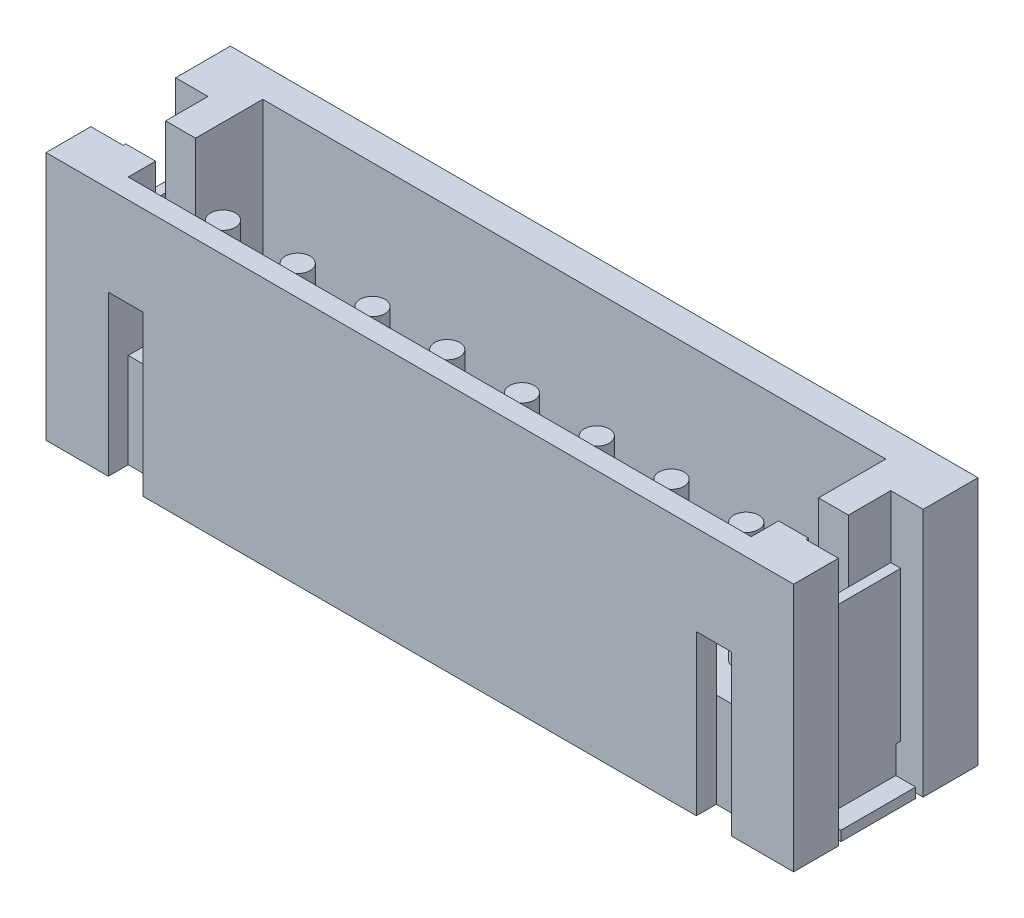
SolidWorks part; units mm, degrees
ref_plane "Front Plane" through (0, 0, 0) normal (0, 0, 1) x (1, 0, 0)
ref_plane "Top Plane" through (0, 0, 0) normal (0, 1, 0) x (1, 0, 0)
ref_plane "Right Plane" through (0, 0, 0) normal (1, 0, 0) x (0, 0, -1)
sketch "Sketch1" plane through (0, 0, 0) normal (0, 0, 1) x (1, 0, 0)
  line L0 (-7.5, 0) -> (-6.25, 0)
  line L1 (-6.25, 0) -> (-6.25, 5)
  line L2 (-6.25, 5) -> (-7.5, 5)
  line L3 (-7.5, 5) -> (-7.5, 0)
extrude "Boss-Extrude1" add sketch "Sketch1" against normal blind 3.1
sketch "Sketch2" plane through (-6.25, 0, 0) normal (1, 0, 0) x (0, 0, -1)
  line L0 (0, 5) -> (0.4, 5)
  line L1 (0.4, 5) -> (0.4, 1.9)
  line L2 (0.4, 1.9) -> (1.75, 1.9)
  line L3 (1.75, 1.9) -> (2.05, 1.6)
  line L4 (2.05, 1.6) -> (3.1, 1.6)
  line L5 (3.1, 0) -> (0, 0)
  line L6 (0, 0) -> (0, 5)
  spline S0 degree 1 poles (3.1, 0) (3.1, 1.6) knots 0 0 0.32 0.32
extrude "Boss-Extrude2" add sketch "Sketch2" along normal blind 12.5
sketch "Sketch3" plane through (6.25, 0, 0) normal (1, 0, 0) x (0, 0, -1)
  line L0 (3.1, 0) -> (0, 0)
  line L1 (0, 0) -> (0, 5)
  line L2 (0, 5) -> (3.1, 5)
  spline S0 degree 1 poles (3.1, 0) (3.1, 5) knots 0 0 1 1
extrude "Boss-Extrude3" add sketch "Sketch3" along normal blind 1.25
ref_plane "Plane1" through (6.25, 0, 0) normal (1, 0, 0) x (0, 0, -1)
sketch "Sketch4" plane through (6.25, 0, 0) normal (1, 0, 0) x (0, 0, -1)
  line L0 (0.4, 1.9) -> (0.4, 3.2)
  line L1 (0.4, 3.2) -> (0, 3.2)
  line L2 (0, 3.2) -> (0, 0)
  line L3 (0, 0) -> (0.4, 0)
  line L4 (0.4, 0) -> (0.4, 1.9)
extrude "Cut-Extrude1" cut sketch "Sketch4" against normal blind 0.7
ref_plane "Plane2" through (-6.25, 0, 0) normal (-1, 0, 0) x (0, -1, 0)
sketch "Sketch5" plane through (-6.25, 0, 0) normal (-1, 0, 0) x (0, -1, 0)
  line L0 (-1.9, -0.4) -> (0, -0.4)
  line L1 (0, -0.4) -> (0, 0)
  line L2 (0, 0) -> (-3.2, 0)
  line L3 (-3.2, 0) -> (-3.2, -0.4)
  line L4 (-3.2, -0.4) -> (-1.9, -0.4)
extrude "Cut-Extrude2" cut sketch "Sketch5" against normal blind 0.7
sketch "Sketch6" plane through (0, 0, -3.1) normal (0, 0, -1) x (-1, 0, 0)
  spline S0 degree 1 poles (7.5, 0) (-7.5, 0) knots 0 0 1 1
  spline S1 degree 1 poles (-7.5, 0) (-7.5, 5) knots 0 0 1 1
  spline S2 degree 1 poles (7.5, 5) (-7.5, 5) knots 0 0 1 1
  spline S3 degree 1 poles (7.5, 0) (7.5, 5) knots 0 0 1 1
extrude "Boss-Extrude4" add sketch "Sketch6" along normal blind 0.6
sketch "Sketch7" plane through (0, 0, 0) normal (0, -1, 0) x (1, 0, 0)
  line L0 (-7.5, -2.6) -> (-7.05, -2.6)
  line L1 (-7.05, -2.6) -> (-7.05, -0.9)
  line L2 (-7.05, -0.9) -> (-7.5, -0.9)
  line L3 (-7.5, -0.9) -> (-7.5, -2.6)
extrude "Cut-Extrude3" cut sketch "Sketch7" against normal through all
sketch "Sketch8" plane through (-7.05, 0, 0) normal (-1, 0, 0) x (0, 0, 1)
  line L0 (-1.75, 5) -> (-1.75, 3.75)
  line L1 (-1.75, 3.75) -> (-0.95, 3.75)
  line L2 (-0.95, 3.75) -> (-0.95, 5)
  line L3 (-0.95, 5) -> (-1.75, 5)
extrude "Cut-Extrude4" cut sketch "Sketch8" against normal up to next
sketch "Sketch9" plane through (-7.05, 0, 0) normal (-1, 0, 0) x (0, 0, 1)
  line L0 (-2.6, 3.75) -> (-1.75, 3.75)
  line L1 (-1.75, 3.75) -> (-1.75, 5)
  line L2 (-1.75, 5) -> (-2.6, 5)
  line L3 (-2.6, 5) -> (-2.6, 3.75)
extrude "Cut-Extrude5" cut sketch "Sketch9" against normal blind 0.2
sketch "Sketch10" plane through (-7.05, 0, 0) normal (-1, 0, 0) x (0, 0, 1)
  line L0 (-0.95, 3.75) -> (-0.9, 3.75)
  line L1 (-0.9, 3.75) -> (-0.9, 5)
  line L2 (-0.9, 5) -> (-0.95, 5)
  line L3 (-0.95, 5) -> (-0.95, 3.75)
extrude "Cut-Extrude6" cut sketch "Sketch10" against normal blind 0.2
ref_plane "Plane3" through (0, 3.75, 0) normal (0, 1, 0) x (1, 0, 0)
ref_plane "Plane4" through (0, 3.2, 0) normal (0, -1, 0) x (1, 0, 0)
sketch "Sketch12" plane through (0, 3.2, 0) normal (0, -1, 0) x (1, 0, 0)
  line L0 (-6.25, -0.95) -> (-6.85, -0.95)
  line L1 (-6.85, -0.95) -> (-6.85, -1.75)
  line L2 (-6.85, -1.75) -> (-6.25, -1.75)
  line L3 (-6.25, -1.75) -> (-6.25, -0.95)
extrude "Cut-Extrude7" cut sketch "Sketch12" against normal up to surface up to plane "Plane3"
sketch "Sketch13" plane through (0, 0, 0) normal (0, -1, 0) x (1, 0, 0)
  line L0 (7.5, -0.9) -> (7.05, -0.9)
  line L1 (7.05, -0.9) -> (7.05, -2.6)
  line L2 (7.05, -2.6) -> (7.5, -2.6)
  line L3 (7.5, -2.6) -> (7.5, -0.9)
extrude "Cut-Extrude8" cut sketch "Sketch13" against normal through all
sketch "Sketch14" plane through (7.05, 0, 0) normal (1, 0, 0) x (0, 0, -1)
  line L0 (0.95, 5) -> (0.95, 3.75)
  line L1 (0.95, 3.75) -> (1.75, 3.75)
  line L2 (1.75, 3.75) -> (1.75, 5)
  line L3 (1.75, 5) -> (0.95, 5)
extrude "Cut-Extrude9" cut sketch "Sketch14" against normal through all
sketch "Sketch15" plane through (7.05, 0, 0) normal (1, 0, 0) x (0, 0, -1)
  line L0 (2.6, 3.75) -> (2.6, 5)
  line L1 (2.6, 5) -> (1.75, 5)
  line L2 (1.75, 5) -> (1.75, 3.75)
  line L3 (1.75, 3.75) -> (2.6, 3.75)
extrude "Cut-Extrude10" cut sketch "Sketch15" against normal blind 0.2
ref_plane "Plane5" through (-7.05, 0, 0) normal (-1, 0, 0) x (0, -1, 0)
ref_plane "Plane6" through (-6.85, 0, 0) normal (1, 0, 0) x (0, 0, -1)
sketch "Sketch17" plane through (-6.85, 0, 0) normal (1, 0, 0) x (0, 0, -1)
  line L0 (1, 0) -> (1, 0.75)
  line L1 (1, 0.75) -> (0.9, 0.75)
  line L2 (0.9, 0.75) -> (0.9, 0)
  line L3 (0.9, 0) -> (1, 0)
extrude "Cut-Extrude11" cut sketch "Sketch17" against normal up to surface up to plane "Plane5"
sketch "Sketch18" plane through (-7.05, 0, 0) normal (-1, 0, 0) x (0, 0, 1)
  line L0 (-1, 0.2) -> (-1, 0)
  line L1 (-1, 0) -> (-2.5, 0)
  line L2 (-2.5, 0) -> (-2.5, 0.2)
  line L3 (-2.5, 0.2) -> (-1, 0.2)
extrude "Boss-Extrude5" add sketch "Sketch18" along normal blind 0.4
sketch "Sketch20" plane through (-6.85, 0, 0) normal (1, 0, 0) x (0, 0, -1)
  line L0 (2.6, 0.75) -> (2.5, 0.75)
  line L1 (2.5, 0.75) -> (2.5, 0)
  line L2 (2.5, 0) -> (2.6, 0)
  line L3 (2.6, 0) -> (2.6, 0.75)
extrude "Cut-Extrude12" cut sketch "Sketch20" against normal up to surface up to plane "Plane5"
ref_plane "Plane7" through (7.05, 0, 0) normal (1, 0, 0) x (0, 0, -1)
ref_plane "Plane8" through (6.85, 0, 0) normal (-1, 0, 0) x (0, -1, 0)
sketch "Sketch22" plane through (6.85, 0, 0) normal (-1, 0, 0) x (0, -1, 0)
  line L0 (0, -2.6) -> (0, -2.5)
  line L1 (0, -2.5) -> (-0.75, -2.5)
  line L2 (-0.75, -2.5) -> (-0.75, -2.6)
  line L3 (-0.75, -2.6) -> (0, -2.6)
extrude "Cut-Extrude13" cut sketch "Sketch22" against normal up to surface up to plane "Plane7"
sketch "Sketch23" plane through (7.05, 0, 0) normal (1, 0, 0) x (0, 0, -1)
  line L0 (1, 0) -> (1, 0.2)
  line L1 (1, 0.2) -> (2.5, 0.2)
  line L2 (2.5, 0.2) -> (2.5, 0)
  line L3 (2.5, 0) -> (1, 0)
extrude "Boss-Extrude6" add sketch "Sketch23" along normal blind 0.4
sketch "Sketch25" plane through (6.85, 0, 0) normal (-1, 0, 0) x (0, -1, 0)
  line L0 (0, -0.9) -> (-0.75, -0.9)
  line L1 (-0.75, -0.9) -> (-0.75, -1)
  line L2 (-0.75, -1) -> (0, -1)
  line L3 (0, -1) -> (0, -0.9)
extrude "Cut-Extrude14" cut sketch "Sketch25" against normal up to surface up to plane "Plane7"
sketch "Sketch26" plane through (7.05, 0, 0) normal (1, 0, 0) x (0, 0, -1)
  line L0 (0.95, 3.75) -> (0.95, 5)
  line L1 (0.95, 5) -> (0.9, 5)
  line L2 (0.9, 5) -> (0.9, 3.75)
  line L3 (0.9, 3.75) -> (0.95, 3.75)
extrude "Cut-Extrude15" cut sketch "Sketch26" against normal blind 0.2
sketch "Sketch28" plane through (0, 3.2, 0) normal (0, -1, 0) x (1, 0, 0)
  line L0 (6.85, -1.75) -> (6.85, -0.95)
  line L1 (6.85, -0.95) -> (6.25, -0.95)
  line L2 (6.25, -0.95) -> (6.25, -1.75)
  line L3 (6.25, -1.75) -> (6.85, -1.75)
extrude "Cut-Extrude16" cut sketch "Sketch28" against normal up to surface up to plane "Plane3"
ref_plane "Plane9" through (0, 0, -1.3) normal (0, 0, -1) x (-1, 0, 0)
sketch "Sketch29" plane through (0, 0, -1.3) normal (0, 0, -1) x (-1, 0, 0)
  line L0 (-5.5, 1.9) -> (-5.25, 1.9)
  line L1 (-5.25, 1.9) -> (-5.25, 4.3)
  line L2 (-5.25, 4.3) -> (-5.5, 4.3)
  line L3 (-5.5, 4.3) -> (-5.5, 1.9)
  line L4 (-5.25, 1.9) -> (-5.25, 4.3) construction
revolve "Revolve1" add sketch "Sketch29" angle 360 about L4
sketch "Sketch30" plane through (0, 0, -1.3) normal (0, 0, -1) x (-1, 0, 0)
  line L0 (-4, 1.9) -> (-3.75, 1.9)
  line L1 (-3.75, 1.9) -> (-3.75, 4.3)
  line L2 (-3.75, 4.3) -> (-4, 4.3)
  line L3 (-4, 4.3) -> (-4, 1.9)
  line L4 (-3.75, 1.9) -> (-3.75, 4.3) construction
revolve "Revolve2" add sketch "Sketch30" angle 360 about L4
sketch "Sketch31" plane through (0, 0, -1.3) normal (0, 0, -1) x (-1, 0, 0)
  line L0 (-2.5, 1.9) -> (-2.25, 1.9)
  line L1 (-2.25, 1.9) -> (-2.25, 4.3)
  line L2 (-2.25, 4.3) -> (-2.5, 4.3)
  line L3 (-2.5, 4.3) -> (-2.5, 1.9)
  line L4 (-2.25, 1.9) -> (-2.25, 4.3) construction
revolve "Revolve3" add sketch "Sketch31" angle 360 about L4
sketch "Sketch32" plane through (0, 0, -1.3) normal (0, 0, -1) x (-1, 0, 0)
  line L0 (-1, 1.9) -> (-0.75, 1.9)
  line L1 (-0.75, 1.9) -> (-0.75, 4.3)
  line L2 (-0.75, 4.3) -> (-1, 4.3)
  line L3 (-1, 4.3) -> (-1, 1.9)
  line L4 (-0.75, 1.9) -> (-0.75, 4.3) construction
revolve "Revolve4" add sketch "Sketch32" angle 360 about L4
sketch "Sketch33" plane through (0, 0, -1.3) normal (0, 0, -1) x (-1, 0, 0)
  line L0 (0.5, 1.9) -> (0.75, 1.9)
  line L1 (0.75, 1.9) -> (0.75, 4.3)
  line L2 (0.75, 4.3) -> (0.5, 4.3)
  line L3 (0.5, 4.3) -> (0.5, 1.9)
  line L4 (0.75, 1.9) -> (0.75, 4.3) construction
revolve "Revolve5" add sketch "Sketch33" angle 360 about L4
sketch "Sketch34" plane through (0, 0, -1.3) normal (0, 0, -1) x (-1, 0, 0)
  line L0 (2, 1.9) -> (2.25, 1.9)
  line L1 (2.25, 1.9) -> (2.25, 4.3)
  line L2 (2.25, 4.3) -> (2, 4.3)
  line L3 (2, 4.3) -> (2, 1.9)
  line L4 (2.25, 1.9) -> (2.25, 4.3) construction
revolve "Revolve6" add sketch "Sketch34" angle 360 about L4
sketch "Sketch35" plane through (0, 0, -1.3) normal (0, 0, -1) x (-1, 0, 0)
  line L0 (3.5, 1.9) -> (3.75, 1.9)
  line L1 (3.75, 1.9) -> (3.75, 4.3)
  line L2 (3.75, 4.3) -> (3.5, 4.3)
  line L3 (3.5, 4.3) -> (3.5, 1.9)
  line L4 (3.75, 1.9) -> (3.75, 4.3) construction
revolve "Revolve7" add sketch "Sketch35" angle 360 about L4
sketch "Sketch36" plane through (0, 0, -1.3) normal (0, 0, -1) x (-1, 0, 0)
  line L0 (5, 1.9) -> (5.25, 1.9)
  line L1 (5.25, 1.9) -> (5.25, 4.3)
  line L2 (5.25, 4.3) -> (5, 4.3)
  line L3 (5, 4.3) -> (5, 1.9)
  line L4 (5.25, 1.9) -> (5.25, 4.3) construction
revolve "Revolve8" add sketch "Sketch36" angle 360 about L4
ref_plane "Plane10" through (0, 0.25, 0) normal (0, -1, 0) x (1, 0, 0)
sketch "Sketch37" plane through (0, 0.25, 0) normal (0, -1, 0) x (1, 0, 0)
  line L0 (5.5, -3.7) -> (5.25, -3.7)
  line L1 (5.25, -3.7) -> (5.25, -5.2)
  line L2 (5.25, -5.2) -> (5.5, -5.2)
  line L3 (5.5, -5.2) -> (5.5, -3.7)
  line L4 (5.25, -3.7) -> (5.25, -5.2) construction
revolve "Revolve9" add sketch "Sketch37" angle 360 about L4
sketch "Sketch38" plane through (0, 0.25, 0) normal (0, -1, 0) x (1, 0, 0)
  line L0 (4, -3.7) -> (3.75, -3.7)
  line L1 (3.75, -3.7) -> (3.75, -5.2)
  line L2 (3.75, -5.2) -> (4, -5.2)
  line L3 (4, -5.2) -> (4, -3.7)
  line L4 (3.75, -3.7) -> (3.75, -5.2) construction
revolve "Revolve10" add sketch "Sketch38" angle 360 about L4
sketch "Sketch39" plane through (0, 0.25, 0) normal (0, -1, 0) x (1, 0, 0)
  line L0 (2.5, -3.7) -> (2.25, -3.7)
  line L1 (2.25, -3.7) -> (2.25, -5.2)
  line L2 (2.25, -5.2) -> (2.5, -5.2)
  line L3 (2.5, -5.2) -> (2.5, -3.7)
  line L4 (2.25, -3.7) -> (2.25, -5.2) construction
revolve "Revolve11" add sketch "Sketch39" angle 360 about L4
sketch "Sketch40" plane through (0, 0.25, 0) normal (0, -1, 0) x (1, 0, 0)
  line L0 (1, -3.7) -> (0.75, -3.7)
  line L1 (0.75, -3.7) -> (0.75, -5.2)
  line L2 (0.75, -5.2) -> (1, -5.2)
  line L3 (1, -5.2) -> (1, -3.7)
  line L4 (0.75, -3.7) -> (0.75, -5.2) construction
revolve "Revolve12" add sketch "Sketch40" angle 360 about L4
sketch "Sketch41" plane through (0, 0.25, 0) normal (0, -1, 0) x (1, 0, 0)
  line L0 (-0.5, -3.7) -> (-0.75, -3.7)
  line L1 (-0.75, -3.7) -> (-0.75, -5.2)
  line L2 (-0.75, -5.2) -> (-0.5, -5.2)
  line L3 (-0.5, -5.2) -> (-0.5, -3.7)
  line L4 (-0.75, -3.7) -> (-0.75, -5.2) construction
revolve "Revolve13" add sketch "Sketch41" angle 360 about L4
sketch "Sketch42" plane through (0, 0.25, 0) normal (0, -1, 0) x (1, 0, 0)
  line L0 (-2, -3.7) -> (-2.25, -3.7)
  line L1 (-2.25, -3.7) -> (-2.25, -5.2)
  line L2 (-2.25, -5.2) -> (-2, -5.2)
  line L3 (-2, -5.2) -> (-2, -3.7)
  line L4 (-2.25, -3.7) -> (-2.25, -5.2) construction
revolve "Revolve14" add sketch "Sketch42" angle 360 about L4
sketch "Sketch43" plane through (0, 0.25, 0) normal (0, -1, 0) x (1, 0, 0)
  line L0 (-3.5, -3.7) -> (-3.75, -3.7)
  line L1 (-3.75, -3.7) -> (-3.75, -5.2)
  line L2 (-3.75, -5.2) -> (-3.5, -5.2)
  line L3 (-3.5, -5.2) -> (-3.5, -3.7)
  line L4 (-3.75, -3.7) -> (-3.75, -5.2) construction
revolve "Revolve15" add sketch "Sketch43" angle 360 about L4
sketch "Sketch44" plane through (0, 0.25, 0) normal (0, -1, 0) x (1, 0, 0)
  line L0 (-5, -3.7) -> (-5.25, -3.7)
  line L1 (-5.25, -3.7) -> (-5.25, -5.2)
  line L2 (-5.25, -5.2) -> (-5, -5.2)
  line L3 (-5, -5.2) -> (-5, -3.7)
  line L4 (-5.25, -3.7) -> (-5.25, -5.2) construction
revolve "Revolve16" add sketch "Sketch44" angle 360 about L4
